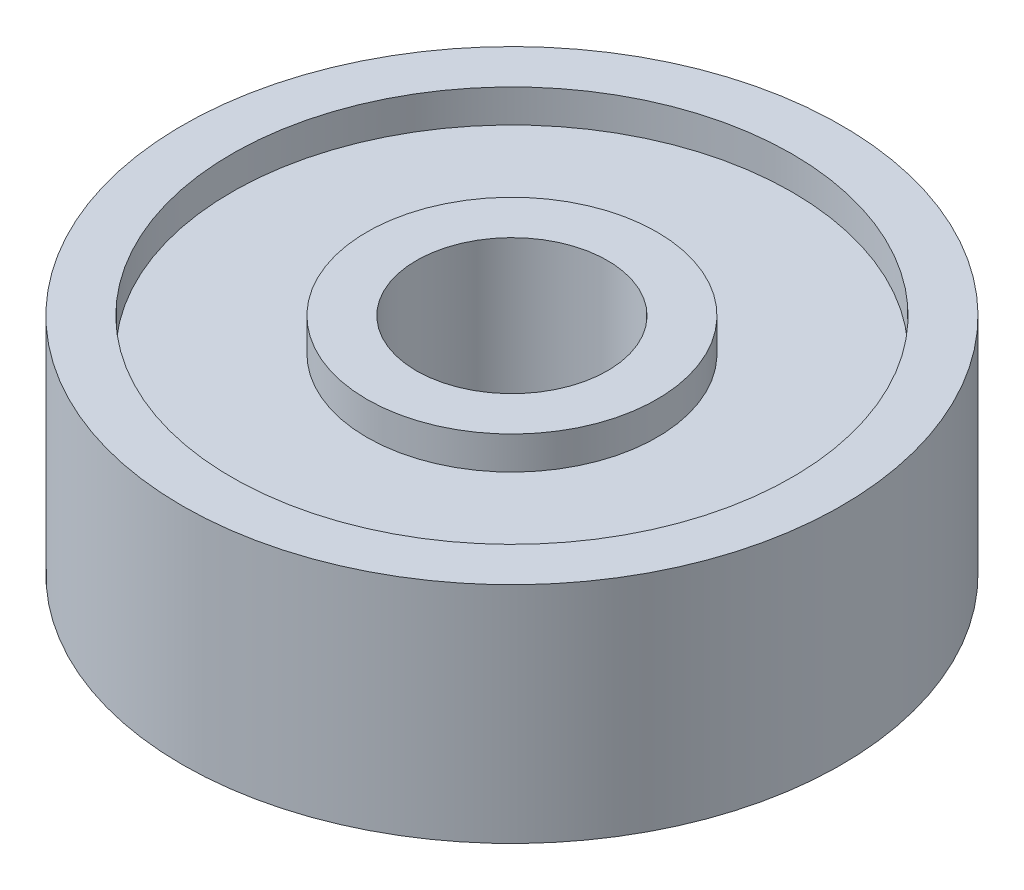
SolidWorks part; units mm, degrees
material "橡胶"
ref_plane "前视基准面" through (0, 0, 0) normal (0, 0, 1) x (1, 0, 0)
ref_plane "上视基准面" through (0, 0, 0) normal (0, 1, 0) x (1, 0, 0)
ref_plane "右视基准面" through (0, 0, 0) normal (1, 0, 0) x (0, 0, -1)
sketch "草图1" plane through (0, 0, 0) normal (0, 1, 0) x (1, 0, 0)
  circle A0 centre (0, 0) radius 100
  circle A1 centre (0, 0) radius 29
  dimension "D1" = 58
  dimension "D2" = 200
extrude "凸台-拉伸1" add sketch "草图1" along normal mid plane 68
sketch "草图2" plane through (0, -34, 0) normal (0, -1, 0) x (1, 0, 0)
  circle A2 centre (0, 0) radius 85
  circle A3 centre (0, 0) radius 85
  circle A4 centre (0, 0) radius 44
  circle A5 centre (0, 0) radius 44
  dimension "D1" = 15
  dimension "D2" = 15
extrude "切除-拉伸1" cut sketch "草图2" against normal blind 10
mirror "镜向1" about plane through (0, 0, 0) normal (0, 1, 0) of "切除-拉伸1"
